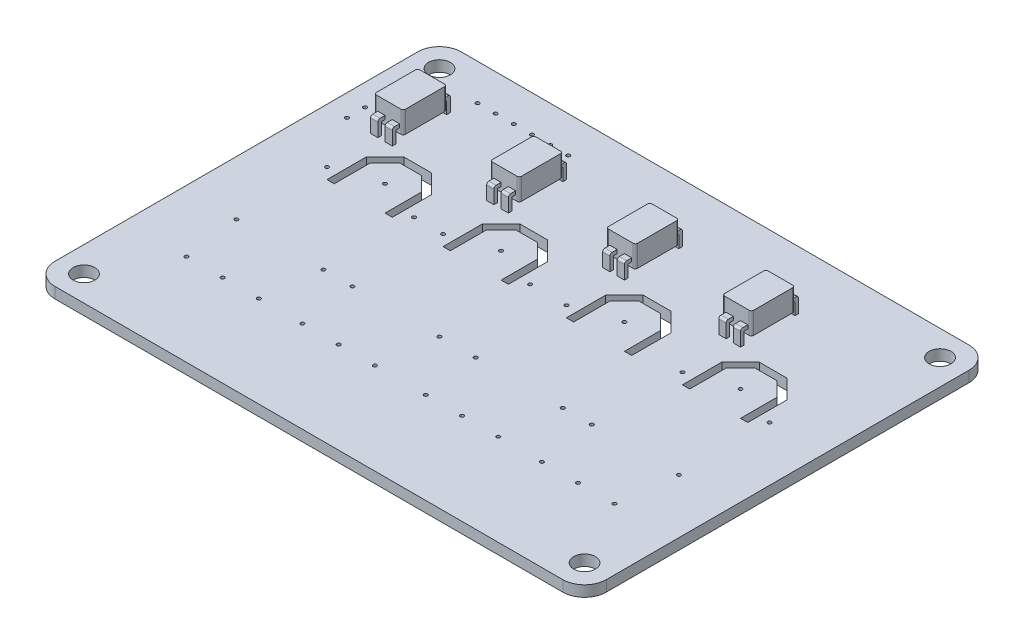
SolidWorks part; units mm, degrees
ref_plane "Ön Düzlem" through (0, 0, 0) normal (0, 0, 1) x (1, 0, 0)
ref_plane "Üst Düzlem" through (0, 0, 0) normal (0, 1, 0) x (1, 0, 0)
ref_plane "Sağ Düzlem" through (0, 0, 0) normal (1, 0, 0) x (0, 0, -1)
sketch "Çizim1" plane through (0, 0, 0) normal (0, 1, 0) x (1, 0, 0)
  line L0 (0, 0) -> (0, 28) construction
  line L1 (-35, 28) -> (35, 28)
  line L2 (-38, 25) -> (-38, -25)
  line L3 (-35, -28) -> (35, -28)
  line L4 (38, 25) -> (38, -25)
  line L5 (-38, 28) -> (38, -28) construction
  line L6 (-38, -28) -> (38, 28) construction
  line L7 (0, 28) -> (0, -28) construction
  line L8 (38, 0) -> (-38, 0) construction
  line L9 (-38, 7) -> (38, 7) construction
  line L10 (1, 28) -> (1, -28) construction
  line L11 (-1, 28) -> (-1, -28) construction
  line L12 (-38, 5) -> (38, 5) construction
  line L13 (-38, -7.5) -> (38, -7.5) construction
  line L14 (-8.5, 7) -> (-8.5, -7.5) construction
  line L15 (-24.5, 7) -> (-24.5, -7.5) construction
  line L16 (-38, -15.39) -> (38, -15.39) construction
  line L17 (-24.5, -7.5) -> (-24.5, -15.39) construction
  line L18 (-8.5, -7.5) -> (-8.5, -15.39) construction
  line L19 (-16.5, -7.5) -> (-16.5, -15.39) construction
  circle A4 centre (-34.5, 24.5) radius 1.5
  circle A5 centre (34.5, 24.5) radius 1.5
  circle A6 centre (34.5, -24.5) radius 1.5
  circle A7 centre (-34.5, -24.5) radius 1.5
  arc A8 (-38, -25) -> (-35, -28) centre (-35, -25) ccw
  arc A9 (35, -28) -> (38, -25) centre (35, -25) ccw
  arc A10 (35, 28) -> (38, 25) centre (35, 25) cw
  arc A11 (-35, 28) -> (-38, 25) centre (-35, 25) ccw
  circle A12 centre (-8.5, 7) radius 0.25
  circle A13 centre (-24.5, 7) radius 0.25
  circle A14 centre (8.5, 7) radius 0.25
  circle A15 centre (24.5, 7) radius 0.25
  circle A16 centre (-14.5, 5) radius 0.25
  circle A17 centre (-18.5, 5) radius 0.25
  circle A18 centre (-14.5, -7.5) radius 0.25
  circle A19 centre (-18.5, -7.5) radius 0.25
  circle A20 centre (-2.5, -7.5) radius 0.25
  circle A21 centre (-2.5, 5) radius 0.25
  circle A22 centre (-30.5, 5) radius 0.25
  circle A23 centre (-30.5, -7.5) radius 0.25
  circle A24 centre (2.5, -7.5) radius 0.25
  circle A25 centre (14.5, -7.5) radius 0.25
  circle A26 centre (18.5, -7.5) radius 0.25
  circle A27 centre (30.5, -7.5) radius 0.25
  circle A28 centre (30.5, 5) radius 0.25
  circle A29 centre (18.5, 5) radius 0.25
  circle A30 centre (2.5, 5) radius 0.25
  circle A31 centre (-24.5, -15.39) radius 0.25
  circle A32 centre (-19.5, -15.39) radius 0.25
  circle A33 centre (-29.5, -15.39) radius 0.25
  circle A34 centre (-13.5, -15.39) radius 0.25
  circle A35 centre (-8.5, -15.39) radius 0.25
  circle A36 centre (-3.5, -15.39) radius 0.25
  circle A37 centre (3.5, -15.39) radius 0.25
  circle A38 centre (8.5, -15.39) radius 0.25
  circle A39 centre (13.5, -15.39) radius 0.25
  circle A40 centre (19.5, -15.39) radius 0.25
  circle A41 centre (24.5, -15.39) radius 0.25
  circle A42 centre (29.5, -15.39) radius 0.25
  point P0 (0, 0)
  point P79 (14.5, 5)
  dimension "D3" = 3
  dimension "D5" = 3.5
  dimension "D4" = 3.5
  dimension "D6" = 3
  dimension "D9" = 0.5
  dimension "D10" = 7.5
  dimension "D11" = 0.5
  dimension "D12" = 16
  dimension "D15" = 6
  dimension "D16" = 6
  dimension "D17" = 6
  dimension "D18" = 6
  dimension "D19" = 6
  dimension "D20" = 6
  dimension "D21" = 6
  dimension "D22" = 6
  dimension "D25" = 0.5
  dimension "D26" = 5
  dimension "D27" = 5
  dimension "D1" = 76
  dimension "D2" = 56
  dimension "D7" = 21
  dimension "D8" = 1
  dimension "D13" = 2
  dimension "D14" = 12.5
  dimension "D23" = 7.89
extrude "Yükseklik-Ekstrüzyon1" add sketch "Çizim1" along normal blind 1.5
sketch "Çizim2" plane through (0, 1.5, 0) normal (0, 1, 0) x (1, 0, 0)
  line L0 (-38, 23) -> (38, 23) construction
  line L1 (-38, 25) -> (-38, -25) construction
  line L2 (38, -25) -> (38, 25) construction
  line L3 (-21.5, 28) -> (-21.5, -28) construction
  line L4 (35, 28) -> (-35, 28) construction
  line L5 (-35, -28) -> (35, -28) construction
  line L6 (-35, 28) -> (-35, -28) construction
  line L7 (-38, 13.5) -> (38, 13.5) construction
  circle A0 centre (-34.5, 24.5) radius 1.5 construction
  circle A1 centre (-22.75, 23) radius 0.25
  circle A2 centre (-25.25, 23) radius 0.25
  circle A3 centre (-27.75, 23) radius 0.25
  circle A4 centre (-20.25, 23) radius 0.25
  circle A5 centre (-17.75, 23) radius 0.25
  circle A6 centre (-15.25, 23) radius 0.25
  circle A7 centre (-35, 14.75) radius 0.25
  circle A8 centre (-35, 12.25) radius 0.25
  dimension "D2" = 0.5
  dimension "D4" = 1.25
  dimension "D5" = 2.5
  dimension "D6" = 2.5
  dimension "D7" = 2.5
  dimension "D8" = 2.5
  dimension "D11" = 0.5
  dimension "D12" = 1.25
  dimension "D13" = 1.25
  dimension "D1" = 16.5
  dimension "D3" = 1.25
  dimension "D9" = 3
  dimension "D10" = 14.5
extrude "Kes-Ekstrüzyon1" cut sketch "Çizim2" against normal blind 10
ref_plane "Düzlem1" through (0, 2.5, 0) normal (0, 1, 0) x (1, 0, 0)
sketch "Çizim3" plane through (0, 2.5, 0) normal (0, 1, 0) x (1, 0, 0)
  line L0 (2, 28) -> (2, -28) construction
  line L1 (-38, 16) -> (38, 16) construction
  line L2 (-38, 25) -> (-38, -25) construction
  line L3 (38, -25) -> (38, 25) construction
  line L4 (35, 28) -> (-35, 28) construction
  line L5 (-30, 28) -> (-30, -28) construction
  line L6 (-35, -28) -> (35, -28) construction
  line L7 (-14, 28) -> (-14, -28) construction
  line L8 (18, 28) -> (18, -28) construction
  line L9 (-22, 16) -> (-22, 20.2346) construction
  line L10 (-31.7, 19) -> (-28.3, 19)
  line L11 (-32, 18.7) -> (-32, 13.3)
  line L12 (-31.7, 13) -> (-28.3, 13)
  line L13 (-28, 18.7) -> (-28, 13.3)
  line L14 (-32, 19) -> (-28, 13) construction
  line L15 (-32, 13) -> (-28, 19) construction
  line L16 (-12.3, 13) -> (-15.7, 13)
  line L17 (-16, 18.7) -> (-16, 13.3)
  line L18 (-12.3, 19) -> (-15.7, 19)
  line L19 (-12, 18.7) -> (-12, 13.3)
  line L20 (-6, 16) -> (-6, 20.8485) construction
  line L21 (0, 18.7) -> (0, 13.3)
  line L22 (0.3, 19) -> (3.7, 19)
  line L23 (4, 18.7) -> (4, 13.3)
  line L24 (0.3, 13) -> (3.7, 13)
  line L25 (19.7, 13) -> (16.3, 13)
  line L26 (16, 18.7) -> (16, 13.3)
  line L27 (19.7, 19) -> (16.3, 19)
  line L28 (20, 18.7) -> (20, 13.3)
  arc A0 (-28.3, 13) -> (-28, 13.3) centre (-28.3, 13.3) ccw
  arc A1 (-28.3, 19) -> (-28, 18.7) centre (-28.3, 18.7) cw
  arc A2 (-32, 13.3) -> (-31.7, 13) centre (-31.7, 13.3) ccw
  arc A3 (-31.7, 19) -> (-32, 18.7) centre (-31.7, 18.7) ccw
  arc A4 (-15.7, 13) -> (-16, 13.3) centre (-15.7, 13.3) cw
  arc A5 (-15.7, 19) -> (-16, 18.7) centre (-15.7, 18.7) ccw
  arc A6 (-12, 13.3) -> (-12.3, 13) centre (-12.3, 13.3) cw
  arc A7 (-12.3, 19) -> (-12, 18.7) centre (-12.3, 18.7) cw
  arc A8 (0, 13.3) -> (0.3, 13) centre (0.3, 13.3) ccw
  arc A9 (0.3, 19) -> (0, 18.7) centre (0.3, 18.7) ccw
  arc A10 (3.7, 19) -> (4, 18.7) centre (3.7, 18.7) cw
  arc A11 (3.7, 13) -> (4, 13.3) centre (3.7, 13.3) ccw
  arc A12 (16.3, 13) -> (16, 13.3) centre (16.3, 13.3) cw
  arc A13 (16.3, 19) -> (16, 18.7) centre (16.3, 18.7) ccw
  arc A14 (20, 13.3) -> (19.7, 13) centre (19.7, 13.3) cw
  arc A15 (19.7, 19) -> (20, 18.7) centre (19.7, 18.7) cw
  point P18 (-30, 16)
  dimension "D8" = 0.3
  dimension "D1" = 12
  dimension "D2" = 8
  dimension "D3" = 16
  dimension "D4" = 16
  dimension "D5" = 16
  dimension "D6" = 4
  dimension "D7" = 6
  dimension "D9" = 8
  dimension "D10" = 8
extrude "Yükseklik-Ekstrüzyon2" add sketch "Çizim3" along normal blind 3 separate body
ref_plane "Düzlem2" through (-31, 0, 0) normal (-1, 0, 0) x (0, 0, 1)
sketch "Çizim4" plane through (-31, 0, 0) normal (-1, 0, 0) x (0, 0, 1)
  line L0 (-16, 2.5) -> (-16, 1.25) construction
  line L1 (-18.7, 2.5) -> (-13.3, 2.5) construction
  line L2 (-25, 0) -> (25, 0) construction
  line L3 (-19.5, 0.8349) -> (-19.5, 3.167)
  line L5 (-20, 0.8349) -> (-20, 3.367)
  line L6 (-19.7, 3.667) -> (-12.3, 3.667)
  line L7 (-12, 0.8349) -> (-12, 3.367)
  line L9 (-20, 3.667) -> (-15.313, 0.8349) construction
  line L10 (-19.5, 3.167) -> (-12.5, 3.167)
  line L11 (-12.5, 0.8349) -> (-12.5, 3.167)
  line L13 (-20, 0.8349) -> (-19.5, 0.8349)
  line L14 (-20, -1.167) -> (-20, 3.667) construction
  line L15 (-19.5, -0.667) -> (-12.5, -0.667) construction
  line L16 (-16.687, 0.8349) -> (-12, 3.667) construction
  line L18 (-12.5, -0.667) -> (-12.5, 3.167) construction
  line L19 (-12, -1.167) -> (-12, 3.667) construction
  line L20 (-20, -1.167) -> (-12, -1.167) construction
  line L21 (-19.5, -0.667) -> (-19.5, 3.167) construction
  line L22 (-12.5, 0.8349) -> (-12, 0.8349)
  line L23 (-16, 0.8349) -> (-16, 0) construction
  line L24 (-20, 3.667) -> (-12, 3.667) construction
  arc A0 (-12.3, 3.667) -> (-12, 3.367) centre (-12.3, 3.367) cw
  arc A1 (-20, 3.367) -> (-19.7, 3.667) centre (-19.7, 3.367) cw
  point P6 (-16, 1.25)
  dimension "D3" = 0.3
  dimension "D1" = 8
  dimension "D2" = 0.5
extrude "Yükseklik-Ekstrüzyon3" add sketch "Çizim4" along normal blind 0.5 and the other way blind 0.5 contours L5 A1 L6 A0 L7 L22 L11 L10 L3 L13
ref_plane "Düzlem3" through (-29, 0, 0) normal (1, 0, 0) x (0, 0, -1)
sketch "Çizim5" plane through (-29, 0, 0) normal (1, 0, 0) x (0, 0, -1)
  line L3 (12.5, 1.5) -> (12.5, 3.167)
  line L5 (12, 1.5) -> (12, 3.367)
  line L6 (12.3, 3.667) -> (19.7, 3.667)
  line L7 (20, 1.5) -> (20, 3.367)
  line L8 (12, 3.667) -> (20, 3.667) construction
  line L9 (12, 3.667) -> (16, 1.25) construction
  line L10 (12.5, 3.167) -> (19.5, 3.167)
  line L11 (19.5, 1.5) -> (19.5, 3.167)
  line L13 (12, 1.5) -> (12.5, 1.5)
  line L14 (12, -1.167) -> (12, 3.667) construction
  line L15 (12.5, -0.667) -> (12.5, 3.167) construction
  line L16 (16, 1.25) -> (20, 3.667) construction
  line L18 (19.5, -0.667) -> (19.5, 3.167) construction
  line L19 (20, -1.167) -> (20, 3.667) construction
  line L20 (12, -1.167) -> (20, -1.167) construction
  line L21 (12.5, -0.667) -> (19.5, -0.667) construction
  line L22 (19.5, 1.5) -> (20, 1.5)
  arc A0 (19.7, 3.667) -> (20, 3.367) centre (19.7, 3.367) cw
  arc A1 (12, 3.367) -> (12.3, 3.667) centre (12.3, 3.367) cw
  point P6 (16, 1.25)
  dimension "D2" = 0.3
  dimension "D1" = 0.5
extrude "Yükseklik-Ekstrüzyon4" add sketch "Çizim5" along normal blind 0.5 and the other way blind 0.5 contours A1 L5 L13 L3 L10 L11 L7 A0 L6
ref_plane "Düzlem4" through (-15, 0, 0) normal (-1, 0, 0) x (0, 0, 1)
sketch "Çizim6" plane through (-15, 0, 0) normal (-1, 0, 0) x (0, 0, 1)
  line L3 (-20, 1.5) -> (-19.5, 1.5)
  line L5 (-20, 1.5) -> (-20, 3.367)
  line L6 (-19.7, 3.667) -> (-12.3, 3.667)
  line L7 (-12, 1.5) -> (-12, 3.367)
  line L9 (-20, 3.667) -> (-16, 1.25) construction
  line L10 (-25, 1.5) -> (25, 1.5) construction
  line L11 (-19.5, 1.5) -> (-19.5, 3.167)
  line L12 (-19.5, 3.167) -> (-12.5, 3.167)
  line L13 (-12.5, 1.5) -> (-12.5, 3.167)
  line L15 (-20, 3.667) -> (-12, 3.667) construction
  line L16 (-12, -1.167) -> (-12, 3.667) construction
  line L17 (-20, -1.167) -> (-20, 3.667) construction
  line L18 (-20, 1.5) -> (-19.5, 1.5)
  line L19 (-19.5, -0.667) -> (-19.5, 3.167) construction
  line L20 (-16, 1.25) -> (-12, 3.667) construction
  line L22 (-12.5, -0.667) -> (-12.5, 3.167) construction
  line L23 (-19.5, -0.667) -> (-12.5, -0.667) construction
  line L24 (-20, -1.167) -> (-12, -1.167) construction
  line L25 (-12.5, 1.5) -> (-12, 1.5)
  line L26 (-12.5, 1.5) -> (-12, 1.5)
  arc A0 (-12.3, 3.667) -> (-12, 3.367) centre (-12.3, 3.367) cw
  arc A1 (-20, 3.367) -> (-19.7, 3.667) centre (-19.7, 3.367) cw
  point P6 (-16, 1.25)
  dimension "D2" = 0.3
  dimension "D1" = 0.5
extrude "Yükseklik-Ekstrüzyon5" add sketch "Çizim6" along normal blind 0.5 and the other way blind 0.5 contours A1 L5 L3 L11 L12 L13 L7 A0 L6
ref_plane "Düzlem5" through (-13, 0, 0) normal (1, 0, 0) x (0, 0, -1)
sketch "Çizim7" plane through (-13, 0, 0) normal (1, 0, 0) x (0, 0, -1)
  line L3 (12.5, 1.5) -> (12.5, 3.167)
  line L5 (12, 1.5) -> (12, 3.367)
  line L6 (12.3, 3.667) -> (19.7, 3.667)
  line L7 (20, 1.5) -> (20, 3.367)
  line L8 (16.4137, 1.5) -> (20, 1.5)
  line L9 (12, 3.667) -> (16, 1.25) construction
  line L10 (12.5, 3.167) -> (19.5, 3.167)
  line L11 (19.5, 1.5) -> (19.5, 3.167)
  line L13 (12, 3.667) -> (20, 3.667) construction
  line L14 (20, -1.167) -> (20, 3.667) construction
  line L15 (12, -1.167) -> (12, 3.667) construction
  line L16 (12, 1.5) -> (12.5, 1.5)
  line L17 (12.5, -0.667) -> (12.5, 3.167) construction
  line L18 (16, 1.25) -> (20, 3.667) construction
  line L20 (19.5, -0.667) -> (19.5, 3.167) construction
  line L21 (12, -1.167) -> (20, -1.167) construction
  line L22 (12.5, -0.667) -> (19.5, -0.667) construction
  arc A0 (19.7, 3.667) -> (20, 3.367) centre (19.7, 3.367) cw
  arc A1 (12, 3.367) -> (12.3, 3.667) centre (12.3, 3.367) cw
  point P6 (16, 1.25)
  dimension "D2" = 0.3
  dimension "D1" = 0.5
extrude "Yükseklik-Ekstrüzyon6" add sketch "Çizim7" along normal blind 0.5 and the other way blind 0.5 contours A1 L5 L16 L3 L10 L11 L8 L7 A0 L6
ref_plane "Düzlem6" through (1, 0, 0) normal (-1, 0, 0) x (0, 0, 1)
sketch "Çizim9" plane through (1, 0, 0) normal (-1, 0, 0) x (0, 0, 1)
  line L3 (-12, 1.5) -> (-12.5, 1.5)
  line L5 (-12, 1.5) -> (-12, 3.367)
  line L6 (-12.3, 3.667) -> (-19.7, 3.667)
  line L7 (-20, 1.5) -> (-20, 3.367)
  line L8 (-15.5435, 1.5) -> (-15.5863, 1.5)
  line L9 (-12, 3.667) -> (-16, 1.25) construction
  line L11 (-12.5, 1.5) -> (-12.5, 3.167)
  line L12 (-12.5, 3.167) -> (-19.5, 3.167)
  line L13 (-19.5, 1.5) -> (-19.5, 3.167)
  line L14 (-16, 1.25) -> (-19.5, 3.167) construction
  line L15 (-12.5, 3.167) -> (-16, 1.25) construction
  line L16 (-16, 1.25) -> (-20, 3.667) construction
  line L17 (-19.5, 1.5) -> (-20, 1.5)
  line L18 (-16.4137, 1.5) -> (-16.4565, 1.5)
  arc A0 (-19.7, 3.667) -> (-20, 3.367) centre (-19.7, 3.367) ccw
  arc A1 (-12, 3.367) -> (-12.3, 3.667) centre (-12.3, 3.367) ccw
  point P6 (-16, 1.25)
  point P11 (-16, 1.25)
  dimension "D1" = 0.3
extrude "Yükseklik-Ekstrüzyon7" add sketch "Çizim9" along normal blind 0.5 and the other way blind 0.5 contours L5 A1 L6 A0 L7 L17 L13 L12 L11 L3
ref_plane "Düzlem7" through (3, 0, 0) normal (1, 0, 0) x (0, 0, -1)
sketch "Çizim10" plane through (3, 0, 0) normal (1, 0, 0) x (0, 0, -1)
  line L0 (19.5, 1.5) -> (20, 1.5)
  line L3 (12, 1.5) -> (12.5, 1.5)
  line L5 (12, 1.5) -> (12, 3.367)
  line L6 (12.3, 3.667) -> (19.7, 3.667)
  line L7 (20, 1.5) -> (20, 3.367)
  line L8 (15.5435, 1.5) -> (15.5863, 1.5)
  line L9 (12, 3.667) -> (16, 1.25) construction
  line L11 (12.5, 1.5) -> (12.5, 3.167)
  line L12 (12.5, 3.167) -> (19.5, 3.167)
  line L13 (19.5, 1.5) -> (19.5, 3.167)
  line L14 (16, 1.25) -> (19.5, 3.167) construction
  line L15 (12.5, 3.167) -> (16, 1.25) construction
  line L16 (16, 1.25) -> (20, 3.667) construction
  line L17 (16.4137, 1.5) -> (16.4565, 1.5)
  arc A0 (19.7, 3.667) -> (20, 3.367) centre (19.7, 3.367) cw
  arc A1 (12, 3.367) -> (12.3, 3.667) centre (12.3, 3.367) cw
  point P6 (16, 1.25)
  point P11 (16, 1.25)
  dimension "D1" = 0.3
extrude "Yükseklik-Ekstrüzyon8" add sketch "Çizim10" along normal blind 0.5 and the other way blind 0.5 contours A1 L5 L3 L11 L12 L13 L0 L7 A0 L6
ref_plane "Düzlem8" through (17, 0, 0) normal (-1, 0, 0) x (0, 0, 1)
sketch "Çizim11" plane through (17, 0, 0) normal (-1, 0, 0) x (0, 0, 1)
  line L0 (-16.4565, 1.5) -> (-16.4137, 1.5)
  line L3 (-20, 1.5) -> (-19.5, 1.5)
  line L5 (-20, 1.5) -> (-20, 3.367)
  line L6 (-19.7, 3.667) -> (-12.3, 3.667)
  line L7 (-12, 1.5) -> (-12, 3.367)
  line L8 (-15.5863, 1.5) -> (-15.5435, 1.5)
  line L9 (-20, 3.667) -> (-16, 1.25) construction
  line L11 (-19.5, 1.5) -> (-19.5, 3.167)
  line L12 (-19.5, 3.167) -> (-12.5, 3.167)
  line L13 (-12.5, 1.5) -> (-12.5, 3.167)
  line L14 (-16, 1.25) -> (-12.5, 3.167) construction
  line L15 (-19.5, 3.167) -> (-16, 1.25) construction
  line L16 (-12, 1.5) -> (-12.5, 1.5) construction
  line L17 (-16, 1.25) -> (-12, 3.667) construction
  line L18 (-12.5, 1.5) -> (-12, 1.5)
  arc A0 (-12.3, 3.667) -> (-12, 3.367) centre (-12.3, 3.367) cw
  arc A1 (-20, 3.367) -> (-19.7, 3.667) centre (-19.7, 3.367) cw
  point P6 (-16, 1.25)
  point P11 (-16, 1.25)
  dimension "D1" = 0.3
extrude "Yükseklik-Ekstrüzyon9" add sketch "Çizim11" along normal blind 0.5 and the other way blind 0.5 contours A1 L5 L3 L11 L12 L13 L18 L7 A0 L6
ref_plane "Düzlem9" through (19, 0, 0) normal (1, 0, 0) x (0, 0, -1)
sketch "Çizim12" plane through (19, 0, 0) normal (1, 0, 0) x (0, 0, -1)
  line L3 (12, 1.5) -> (12.5, 1.5)
  line L5 (12, 1.5) -> (12, 3.367)
  line L6 (12.3, 3.667) -> (19.7, 3.667)
  line L7 (20, 1.5) -> (20, 3.367)
  line L8 (15.5435, 1.5) -> (15.5863, 1.5)
  line L9 (12, 3.667) -> (16, 1.25) construction
  line L11 (12.5, 1.5) -> (12.5, 3.167)
  line L12 (12.5, 3.167) -> (19.5, 3.167)
  line L13 (19.5, 1.5) -> (19.5, 3.167)
  line L14 (16, 1.25) -> (19.5, 3.167) construction
  line L15 (12.5, 3.167) -> (16, 1.25) construction
  line L16 (16, 1.25) -> (20, 3.667) construction
  line L17 (19.5, 1.5) -> (20, 1.5)
  line L18 (16.4137, 1.5) -> (16.4565, 1.5)
  arc A0 (19.7, 3.667) -> (20, 3.367) centre (19.7, 3.367) cw
  arc A1 (12, 3.367) -> (12.3, 3.667) centre (12.3, 3.367) cw
  point P6 (16, 1.25)
  point P11 (16, 1.25)
  dimension "D1" = 0.3
extrude "Yükseklik-Ekstrüzyon10" add sketch "Çizim12" along normal blind 0.5 and the other way blind 0.5 contours A1 L5 L3 L11 L12 L13 L17 L7 A0 L6
sketch "Çizim13" plane through (0, 1.5, 0) normal (0, 1, 0) x (1, 0, 0)
  line L0 (0, 0) -> (0, 28) construction
  line L1 (35, 28) -> (-35, 28) construction
  line L2 (0, 28) -> (0, 0) construction
  line L3 (0, 0) -> (-38, 0) construction
  line L4 (-38, 25) -> (-38, -25) construction
  line L5 (-16.5, 0) -> (-16.5, 9.6213) construction
  line L6 (-28, 8.5) -> (-26, 10.5)
  line L7 (-26, 10.5) -> (-23, 10.5)
  line L8 (-28, 8.5) -> (-28, 3.5)
  line L10 (-21, 8.5) -> (-21, 3.5)
  line L11 (-28, 10.5) -> (-21, 3.5) construction
  line L12 (-28, 3.5) -> (-21, 10.5) construction
  line L13 (-23, 10.5) -> (-21, 8.5)
  line L14 (-29, 8.9142) -> (-29, 3.5)
  line L16 (-20, 8.9142) -> (-20, 3.5)
  line L17 (-22.5858, 11.5) -> (-20, 8.9142)
  line L18 (-26.4142, 11.5) -> (-22.5858, 11.5)
  line L19 (-29, 8.9142) -> (-26.4142, 11.5)
  line L20 (-29, 3.5) -> (-28, 3.5)
  line L21 (-29, 8.9142) -> (-29, 2.5) construction
  line L22 (-29, 2.5) -> (-20, 2.5) construction
  line L23 (-20, 8.9142) -> (-20, 2.5) construction
  line L24 (-28, 3.5) -> (-21, 3.5) construction
  line L25 (-21, 3.5) -> (-20, 3.5)
  line L26 (-5, 8.5) -> (-7, 10.5)
  line L27 (-7, 10.5) -> (-10, 10.5)
  line L28 (-10, 10.5) -> (-12, 8.5)
  line L29 (-12, 8.5) -> (-12, 3.5)
  line L30 (-12, 3.5) -> (-13, 3.5)
  line L31 (-13, 8.9142) -> (-13, 3.5)
  line L32 (-10.4142, 11.5) -> (-13, 8.9142)
  line L33 (-6.5858, 11.5) -> (-10.4142, 11.5)
  line L34 (-4, 8.9142) -> (-6.5858, 11.5)
  line L35 (-4, 8.9142) -> (-4, 3.5)
  line L36 (-4, 3.5) -> (-5, 3.5)
  line L37 (-5, 8.5) -> (-5, 3.5)
  line L38 (5, 8.5) -> (5, 3.5)
  line L39 (4, 3.5) -> (5, 3.5)
  line L40 (4, 8.9142) -> (4, 3.5)
  line L41 (4, 8.9142) -> (6.5858, 11.5)
  line L42 (6.5858, 11.5) -> (10.4142, 11.5)
  line L43 (10.4142, 11.5) -> (13, 8.9142)
  line L44 (13, 8.9142) -> (13, 3.5)
  line L45 (12, 3.5) -> (13, 3.5)
  line L46 (12, 8.5) -> (12, 3.5)
  line L47 (10, 10.5) -> (12, 8.5)
  line L48 (7, 10.5) -> (10, 10.5)
  line L49 (5, 8.5) -> (7, 10.5)
  line L50 (28, 8.5) -> (26, 10.5)
  line L51 (26, 10.5) -> (23, 10.5)
  line L52 (23, 10.5) -> (21, 8.5)
  line L53 (21, 8.5) -> (21, 3.5)
  line L54 (21, 3.5) -> (20, 3.5)
  line L55 (20, 8.9142) -> (20, 3.5)
  line L56 (22.5858, 11.5) -> (20, 8.9142)
  line L57 (26.4142, 11.5) -> (22.5858, 11.5)
  line L58 (29, 8.9142) -> (26.4142, 11.5)
  line L59 (29, 8.9142) -> (29, 3.5)
  line L60 (29, 3.5) -> (28, 3.5)
  line L61 (28, 8.5) -> (28, 3.5)
  circle A0 centre (-24.5, 7) radius 0.25 construction
  point P14 (-24.5, 7)
  dimension "D1" = 8
  dimension "D2" = 7
  dimension "D3" = 7
  dimension "D4" = 1
extrude "Kes-Ekstrüzyon2" cut sketch "Çizim13" against normal blind 10
